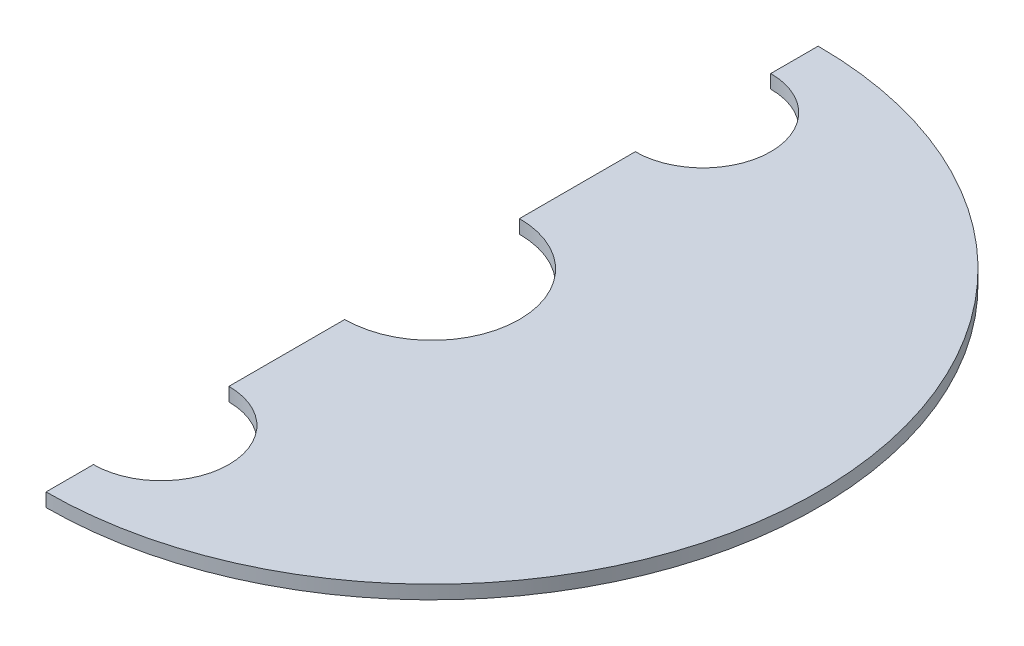
SolidWorks part; units mm, degrees
ref_plane "Front Plane" through (0, 0, 0) normal (0, 0, 1) x (1, 0, 0)
ref_plane "Top Plane" through (0, 0, 0) normal (0, 1, 0) x (1, 0, 0)
ref_plane "Right Plane" through (0, 0, 0) normal (1, 0, 0) x (0, 0, -1)
sketch "Sketch1" plane through (0, 0, 0) normal (0, 1, 0) x (1, 0, 0)
  line L0 (0, 6.45) -> (0, 15)
  line L1 (0, 28.5) -> (0, 25)
  line L2 (0, -6.45) -> (0, -15)
  line L3 (0, -25) -> (0, -28.5)
  line L4 (0, 25) -> (0, 28.5)
  line L5 (0, 15) -> (0, 6.45)
  arc A0 (0, -28.5) -> (0, 28.5) centre (0, 0) ccw
  arc A1 (0, -6.45) -> (0, 6.45) centre (0, 0) ccw
  arc A2 (0, -25) -> (0, -15) centre (0, -20) ccw
  arc A3 (0, 15) -> (0, 25) centre (0, 20) ccw
  dimension "D1" = 57
  dimension "D2" = 12.9
  dimension "D3" = 10
  dimension "D6" = 10
  dimension "D4" = 20
  dimension "D5" = 20
extrude "Boss-Extrude1" add sketch "Sketch1" along normal blind 1 contours A1 L2 A0 L0
